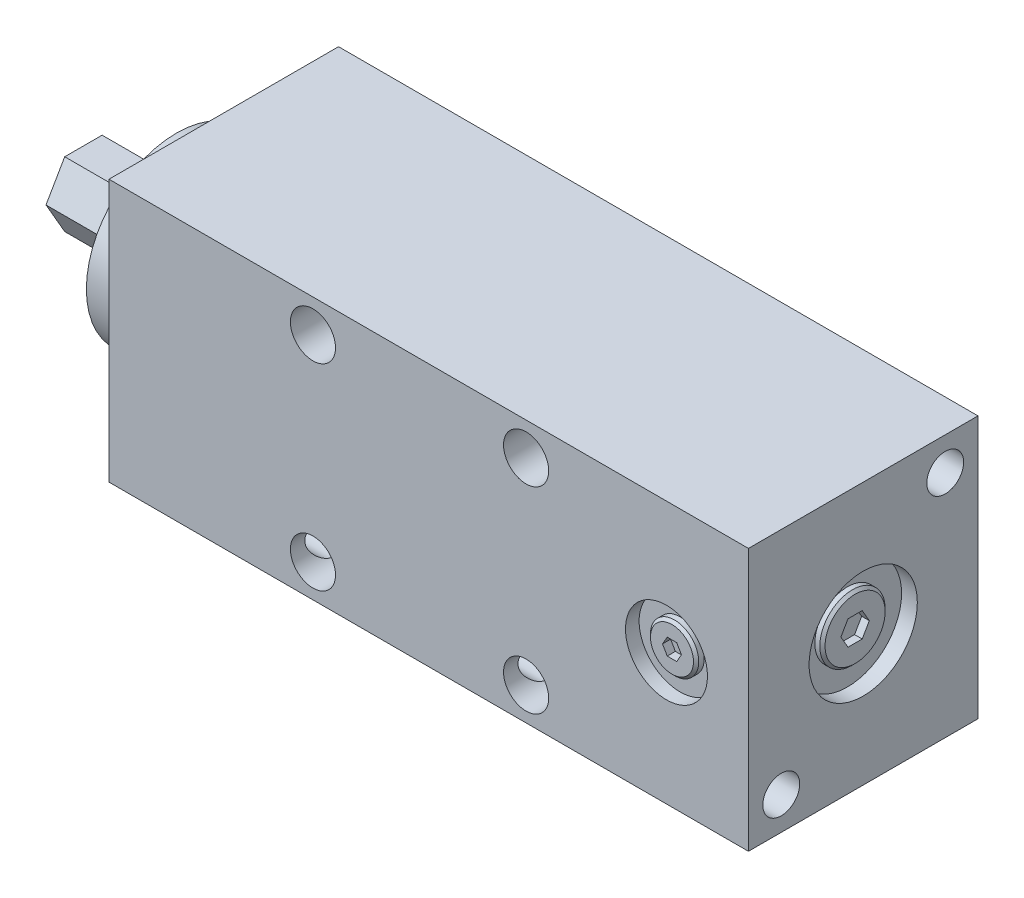
SolidWorks part; units mm, degrees
material "Alloy Steel"
ref_plane "Front Plane" through (0, 0, 0) normal (0, 0, 1) x (1, 0, 0)
ref_plane "Top Plane" through (0, 0, 0) normal (0, 1, 0) x (1, 0, 0)
ref_plane "Right Plane" through (0, 0, 0) normal (1, 0, 0) x (0, 0, -1)
sketch "Sketch1" plane through (0, 0, 0) normal (0, 1, 0) x (1, 0, 0)
  line L1 (0, 0) -> (-123.825, 0)
  line L2 (0, 0) -> (0, 44.45)
  line L3 (0, 44.45) -> (-123.825, 44.45)
  line L4 (-123.825, 0) -> (-123.825, 44.45)
  dimension "D1" = 123.825
  dimension "D2" = 44.45
extrude "Boss-Extrude1" add sketch "Sketch1" along normal blind 50.8
sketch "Sketch2" plane through (-123.825, 0, 0) normal (-1, 0, 0) x (0, 0, 1)
  line L0 (-44.45, 50.8) -> (0, 50.8) construction
  line L1 (-44.45, 50.8) -> (-44.45, 0) construction
  circle A0 centre (-22.225, 25.4) radius 17.4625
  dimension "D3" = 34.925
  dimension "D1" = 25.4
  dimension "D2" = 22.225
extrude "Boss-Extrude2" add sketch "Sketch2" along normal blind 9.144
sketch "Sketch3" plane through (-132.969, 0, 0) normal (-1, 0, 0) x (0, 0, 1)
  line L1 (-44.45, 50.8) -> (0, 50.8) construction
  line L2 (-29.4694, 25.4) -> (-25.8472, 19.1262)
  line L3 (-25.8472, 19.1262) -> (-18.6028, 19.1262)
  line L4 (-18.6028, 19.1262) -> (-14.9806, 25.4)
  line L5 (-14.9806, 25.4) -> (-18.6028, 31.6738)
  line L6 (-18.6028, 31.6738) -> (-25.8472, 31.6738)
  line L8 (-25.8472, 31.6738) -> (-29.4694, 25.4)
  line L9 (-44.45, 50.8) -> (-44.45, 0) construction
  circle A0 centre (-22.225, 25.4) radius 6.2738 construction
  dimension "D1" = 25.4
  dimension "D2" = 22.225
  dimension "D3" = 12.5476
  dimension "D4" = 30
extrude "Boss-Extrude3" add sketch "Sketch3" along normal blind 18.034
sketch "Sketch4" plane through (0, 0, -44.45) normal (0, 0, -1) x (-1, 0, 0)
  line L0 (123.825, 50.8) -> (123.825, 0) construction
  line L1 (0, 0) -> (123.825, 0) construction
  circle A0 centre (84.328, 6.35) radius 4.3688
  circle A1 centre (43.053, 6.35) radius 4.3688
  circle A2 centre (43.053, 44.45) radius 4.3688
  circle A3 centre (84.328, 44.45) radius 4.3688
  dimension "D3" = 8.7376
  dimension "D1" = 39.497
  dimension "D2" = 41.275
  dimension "D4" = 6.35
  dimension "D5" = 38.1
extrude "Cut-Extrude1" cut sketch "Sketch4" against normal through all
sketch "Sketch5" plane through (-123.825, 0, 0) normal (-1, 0, 0) x (0, 0, 1)
  line L0 (-44.45, 0) -> (0, 0) construction
  line L1 (0, 50.8) -> (0, 0) construction
  circle A0 centre (-6.35, 6.35) radius 3.5687
  circle A1 centre (-38.1, 44.45) radius 3.5687
  dimension "D5" = 7.1374
  dimension "D1" = 38.1
  dimension "D2" = 6.35
  dimension "D3" = 31.75
  dimension "D4" = 6.35
extrude "Cut-Extrude2" cut sketch "Sketch5" against normal through all
sketch "Sketch6" plane through (0, 0, 0) normal (0, -1, 0) x (1, 0, 0)
  line L0 (-123.825, -44.45) -> (-123.825, 0) construction
  line L1 (0, -44.45) -> (-123.825, -44.45) construction
  circle A0 centre (-15.875, -22.225) radius 10.4775
  dimension "D1" = 20.955
  dimension "D2" = 107.95
  dimension "D3" = 22.225
extrude "Cut-Extrude3" cut sketch "Sketch6" against normal blind 0.508
sketch "Sketch7" plane through (0, 0, 0) normal (1, 0, 0) x (0, 0, -1)
  line L0 (0, 50.8) -> (44.45, 50.8) construction
  line L2 (44.45, 50.8) -> (44.45, 0) construction
  circle A0 centre (22.225, 25.4) radius 10.4775
  dimension "D3" = 20.955
  dimension "D1" = 25.4
  dimension "D2" = 22.225
extrude "Cut-Extrude4" cut sketch "Sketch7" against normal blind 3.048
sketch "Sketch8" plane through (0, 0, 0) normal (0, 0, 1) x (1, 0, 0)
  line L0 (-123.825, 50.8) -> (-123.825, 0) construction
  line L1 (-123.825, 0) -> (0, 0) construction
  circle A0 centre (-15.875, 25.4) radius 7.9375
  dimension "D1" = 15.875
  dimension "D2" = 107.95
  dimension "D3" = 25.4
extrude "Cut-Extrude5" cut sketch "Sketch8" against normal blind 2.6416
sketch "Sketch9" plane through (0, 0.508, 0) normal (0, -1, 0) x (1, 0, 0)
  circle A0 centre (-15.875, -22.225) radius 6.0706
  dimension "D1" = 12.1412
extrude "Boss-Extrude4" add sketch "Sketch9" along normal blind 1.4732
sketch "Sketch10" plane through (0, -0.9652, 0) normal (0, -1, 0) x (1, 0, 0)
  line L0 (-123.825, 0) -> (0, 0) construction
  line L1 (-15.875, -19.4754) -> (-18.2562, -20.8502)
  line L2 (-18.2562, -20.8502) -> (-18.2562, -23.5998)
  line L3 (-18.2562, -23.5998) -> (-15.875, -24.9746)
  line L4 (-15.875, -24.9746) -> (-13.4937, -23.5998)
  line L5 (-13.4937, -23.5998) -> (-13.4937, -20.8502)
  line L6 (-13.4937, -20.8502) -> (-15.875, -19.4754)
  circle A0 centre (-15.875, -22.225) radius 2.3812 construction
  dimension "D1" = 4.7625
  dimension "D2" = 30
extrude "Cut-Extrude6" cut sketch "Sketch10" against normal blind 1.4732
sketch "Sketch11" plane through (-3.048, 0, 0) normal (1, 0, 0) x (0, 0, -1)
  line L0 (0, 50.8) -> (0, 0) construction
  line L1 (0, 50.8) -> (44.45, 50.8) construction
  line L3 (19.4754, 25.4) -> (20.8502, 23.0188)
  line L4 (20.8502, 23.0188) -> (23.5998, 23.0188)
  line L5 (23.5998, 23.0188) -> (24.9746, 25.4)
  line L6 (24.9746, 25.4) -> (23.5998, 27.7813)
  line L7 (23.5998, 27.7813) -> (20.8502, 27.7813)
  line L8 (20.8502, 27.7813) -> (19.4754, 25.4)
  circle A0 centre (22.225, 25.4) radius 6.3246
  circle A1 centre (22.225, 25.4) radius 2.3812 construction
  dimension "D3" = 12.6492
  dimension "D1" = 22.225
  dimension "D2" = 25.4
  dimension "D4" = 30
  dimension "D5" = 4.7625
extrude "Boss-Extrude5" add sketch "Sketch11" along normal blind 1.4732
sketch "Sketch12" plane through (0, 0, -2.6416) normal (0, 0, 1) x (1, 0, 0)
  line L0 (-123.825, 50.8) -> (0, 50.8) construction
  line L1 (-17.7081, 25.4) -> (-16.7915, 23.8125)
  line L2 (-16.7915, 23.8125) -> (-14.9585, 23.8125)
  line L3 (-14.9585, 23.8125) -> (-14.0419, 25.4)
  line L4 (-14.0419, 25.4) -> (-14.9585, 26.9875)
  line L5 (-14.9585, 26.9875) -> (-16.7915, 26.9875)
  line L6 (-16.7915, 26.9875) -> (-17.7081, 25.4)
  circle A0 centre (-15.875, 25.4) radius 4.6736
  circle A1 centre (-15.875, 25.4) radius 1.5875 construction
  dimension "D1" = 9.3472
  dimension "D2" = 60
  dimension "D3" = 3.175
extrude "Boss-Extrude6" add sketch "Sketch12" along normal blind 1.5748
chamfer "Chamfer1" distance 0.508 angle 45 1 edges at (-15.875, -0.9652, -28.2956)
chamfer "Chamfer2" distance 0.508 angle 45 1 edges at (-1.5748, 25.4, -28.5496)
chamfer "Chamfer3" distance 0.508 angle 45 1 edges at (-11.2014, 25.4, -1.0668)
sketch "Sketch13" plane through (-151.003, 0, 0) normal (-1, 0, 0) x (0, 0, 1)
  line L0 (0, 50.8) -> (0, 0) construction
  line L1 (-44.45, 50.8) -> (0, 50.8) construction
  circle A0 centre (-22.225, 25.4) radius 2.6543
  dimension "D3" = 5.3086
  dimension "D1" = 22.225
  dimension "D2" = 25.4
extrude "Cut-Extrude7" cut sketch "Sketch13" against normal blind 12.7
